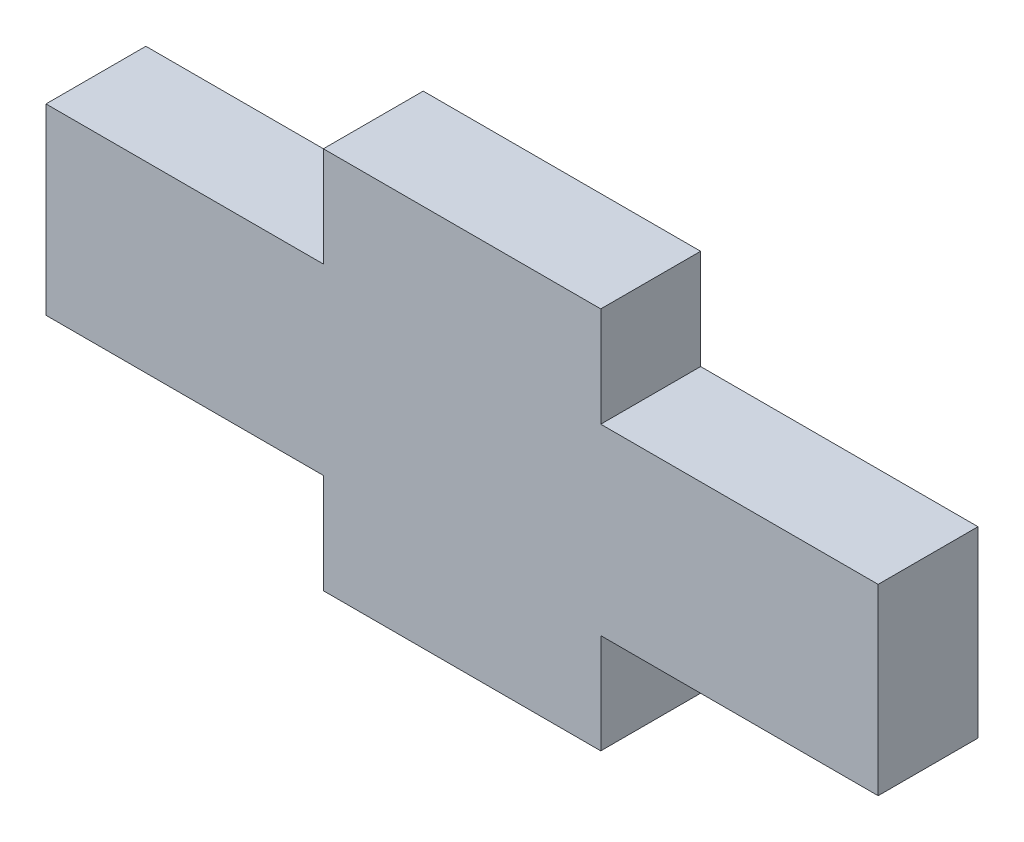
SolidWorks part; units mm, degrees
ref_plane "Front Plane" through (0, 0, 0) normal (0, 0, 1) x (1, 0, 0)
ref_plane "Top Plane" through (0, 0, 0) normal (0, 1, 0) x (1, 0, 0)
ref_plane "Right Plane" through (0, 0, 0) normal (1, 0, 0) x (0, 0, -1)
sketch "Sketch1" plane through (0, 0, 0) normal (0, 0, 1) x (1, 0, 0)
  line L0 (33.8667, 11.176) -> (50.8, 11.176)
  line L1 (0, 0) -> (16.9333, 0)
  line L2 (0, 0) -> (0, 11.176)
  line L3 (0, 11.176) -> (16.9333, 11.176)
  line L4 (50.8, 0) -> (50.8, 11.176)
  line L5 (33.8667, 0) -> (50.8, 0)
  line L6 (16.9333, 11.176) -> (16.9333, 17.272)
  line L7 (16.9333, 17.272) -> (33.8667, 17.272)
  line L8 (33.8667, 11.176) -> (33.8667, 17.272)
  line L10 (16.9333, 0) -> (16.9333, -6.096)
  line L11 (16.9333, -6.096) -> (33.8667, -6.096)
  line L12 (33.8667, 0) -> (33.8667, -6.096)
  dimension "D1" = 50.8
  dimension "D2" = 11.176
  dimension "D3" = 6.096
  dimension "D4" = 6.096
extrude "Boss-Extrude1" add sketch "Sketch1" along normal blind 6.096
equation "\"mat\" = \"mat@fsc.assembly\""
equation "\"D2@Sketch1\"= \"mat\" + .2"
equation "\"D3@Sketch1\"= \"mat\""
equation "\"D4@Sketch1\"= \"mat\""
equation "\"D1@Boss-Extrude1\"= \"mat\""
